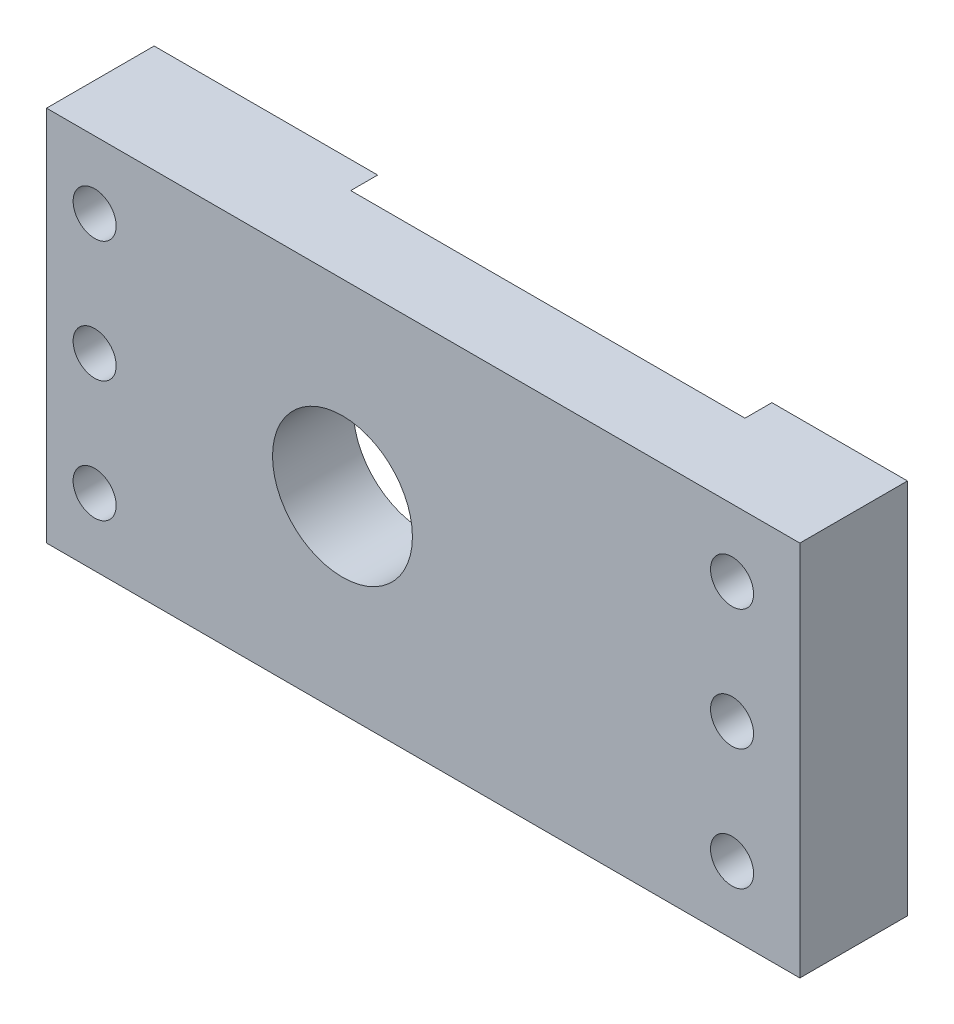
SolidWorks part; units mm, degrees
ref_plane "Front Plane" through (0, 0, 0) normal (0, 0, 1) x (1, 0, 0)
ref_plane "Top Plane" through (0, 0, 0) normal (0, 1, 0) x (1, 0, 0)
ref_plane "Right Plane" through (0, 0, 0) normal (1, 0, 0) x (0, 0, -1)
sketch "Sketch1" plane through (0, 0, 0) normal (0, 0, 1) x (1, 0, 0)
  line L0 (0, 0) -> (31.6607, 0) construction
  line L1 (-70, -35) -> (70, -35)
  line L2 (-70, -35) -> (-70, 35)
  line L3 (-70, 35) -> (70, 35)
  line L4 (70, -35) -> (70, 35)
  line L5 (-70, -35) -> (70, 35) construction
  line L6 (-70, 35) -> (70, -35) construction
  circle A1 centre (-15, 0) radius 13
  circle A2 centre (57.4, 0) radius 4
  circle A3 centre (57.4, 22.5) radius 4
  circle A4 centre (-61.06, 0) radius 4
  circle A5 centre (-61.06, 22.5) radius 4
  circle A6 centre (-61.06, -22.5) radius 4
  circle A7 centre (57.4, -22.5) radius 4
  point P0 (0, 0)
  dimension "D4" = 55
  dimension "D5" = 8
  dimension "D6" = 26
  dimension "D7" = 8.6
  dimension "D9" = 118.46
  dimension "D1" = 140
  dimension "D2" = 70
  dimension "D3" = 15
  dimension "D8" = 45
extrude "Boss-Extrude1" add sketch "Sketch1" along normal mid plane 20
sketch "Sketch2" plane through (0, 0, -10) normal (0, 0, -1) x (-1, 0, 0)
  line L0 (15, -37.5) -> (-44.8, -37.5)
  line L1 (-44.8, -37.5) -> (-44.8, 37.5)
  line L2 (-44.8, 37.5) -> (15, 37.5)
  line L3 (-70, -35) -> (-70, 35) construction
  arc A0 (15, -37.5) -> (15, 37.5) centre (15, 0) ccw
  circle A1 centre (15, 0) radius 13 construction
  dimension "D1" = 75
  dimension "D2" = 25.2
extrude "Cut-Extrude1" cut sketch "Sketch2" against normal blind 5
